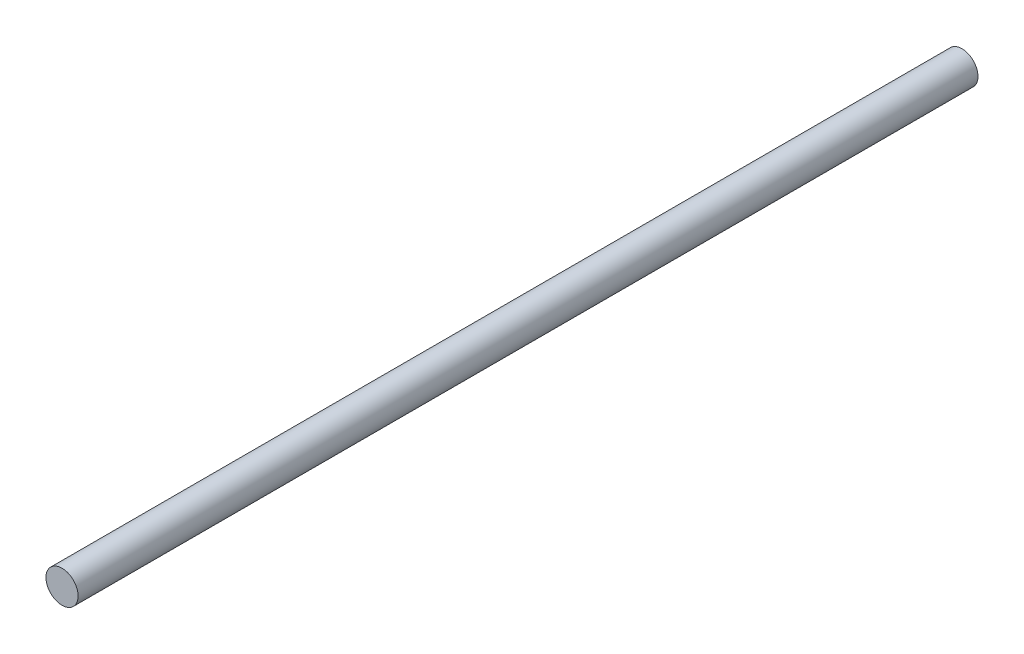
SolidWorks part; units mm, degrees
ref_plane "Front Plane" through (0, 0, 0) normal (0, 0, 1) x (1, 0, 0)
ref_plane "Top Plane" through (0, 0, 0) normal (0, 1, 0) x (1, 0, 0)
ref_plane "Right Plane" through (0, 0, 0) normal (1, 0, 0) x (0, 0, -1)
sketch "Sketch1" plane through (0, 0, 0) normal (0, 0, 1) x (1, 0, 0)
  circle A0 centre (0, 0) radius 2.5
  dimension "D1" = 5
extrude "Boss-Extrude1" add sketch "Sketch1" along normal blind 140
